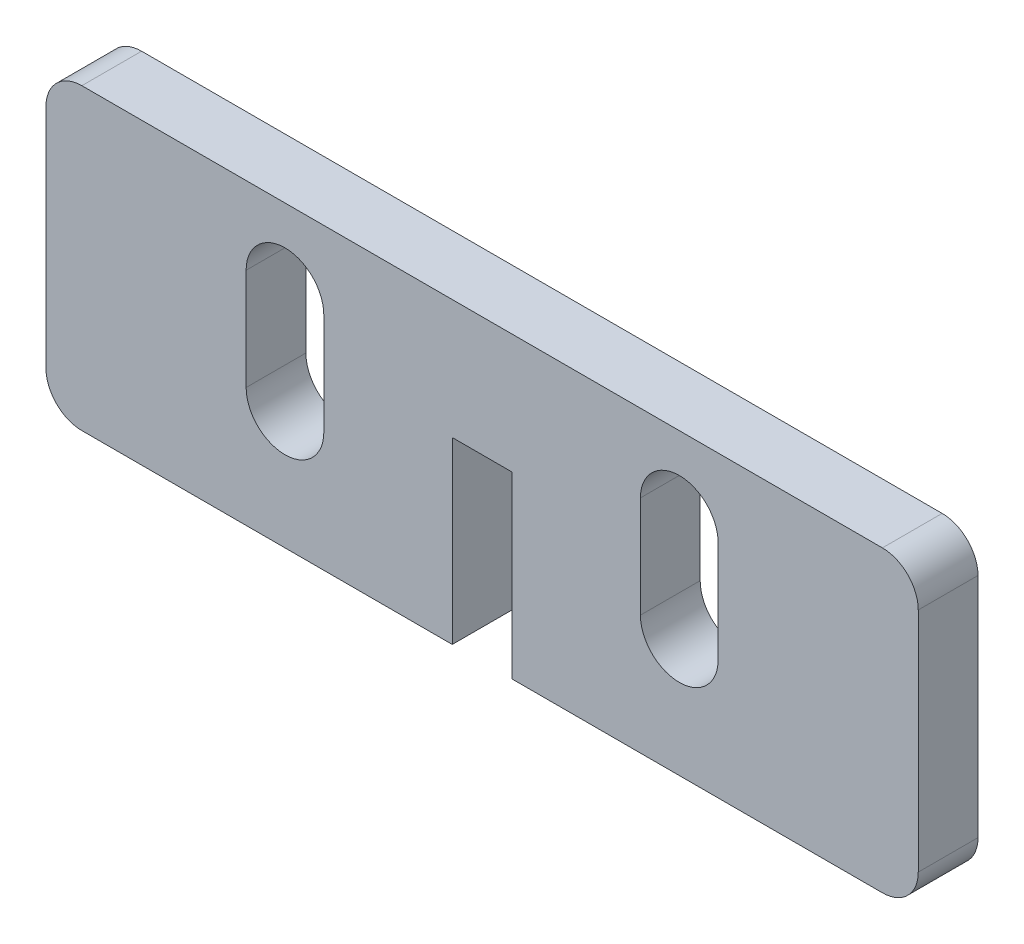
SolidWorks part; units mm, degrees
ref_plane "前视基准面" through (0, 0, 0) normal (0, 0, 1) x (1, 0, 0)
ref_plane "上视基准面" through (0, 0, 0) normal (0, 1, 0) x (1, 0, 0)
ref_plane "右视基准面" through (0, 0, 0) normal (1, 0, 0) x (0, 0, -1)
sketch "草图1" plane through (0, 0, 0) normal (0, 0, 1) x (1, 0, 0)
  line L0 (-16.5, -2.5) -> (-16.5, 6) construction
  line L1 (33.5, -12.5) -> (-33.5, -12.5) construction
  line L2 (36.5, -9.5) -> (36.5, 9.5)
  line L3 (33.5, 12.5) -> (-33.5, 12.5)
  line L4 (-36.5, -9.5) -> (-36.5, 9.5)
  line L5 (0, 12.5) -> (0, -12.5) construction
  line L6 (36.5, 0) -> (-36.5, 0) construction
  line L7 (2.5, 2.5) -> (-2.5, 2.5)
  line L8 (2.5, 2.5) -> (2.5, -12.5)
  line L9 (2.5, -12.5) -> (-2.5, -12.5) construction
  line L10 (-2.5, 2.5) -> (-2.5, -12.5)
  line L11 (0, -12.5) -> (0, 2.5) construction
  line L12 (2.5, -5) -> (-2.5, -5) construction
  line L13 (-19.75, -2.5) -> (-19.75, 6)
  line L14 (-13.25, -2.5) -> (-13.25, 6)
  line L15 (16.5, -2.5) -> (16.5, 6) construction
  line L16 (19.75, -2.5) -> (19.75, 6)
  line L17 (13.25, -2.5) -> (13.25, 6)
  line L18 (-33.5, -12.5) -> (-2.5, -12.5)
  line L19 (2.5, -12.5) -> (33.5, -12.5)
  arc A0 (-19.75, -2.5) -> (-13.25, -2.5) centre (-16.5, -2.5) ccw
  arc A1 (-13.25, 6) -> (-19.75, 6) centre (-16.5, 6) ccw
  arc A2 (19.75, -2.5) -> (13.25, -2.5) centre (16.5, -2.5) cw
  arc A3 (13.25, 6) -> (19.75, 6) centre (16.5, 6) cw
  arc A4 (33.5, -12.5) -> (36.5, -9.5) centre (33.5, -9.5) ccw
  arc A5 (-33.5, -12.5) -> (-36.5, -9.5) centre (-33.5, -9.5) cw
  arc A6 (36.5, 9.5) -> (33.5, 12.5) centre (33.5, 9.5) ccw
  arc A7 (-33.5, 12.5) -> (-36.5, 9.5) centre (-33.5, 9.5) ccw
  point P0 (0, 0)
  point P4 (0, -5)
  point P13 (-16.5, 1.75)
  point P21 (-16.5, 9.25)
  point P22 (-16.5, -5.75)
  point P25 (16.5, 1.75)
  point P32 (36.5, -12.5)
  point P37 (36.5, 12.5)
  point P40 (-36.5, 12.5)
  dimension "D9" = 3
  dimension "D1" = 73
  dimension "D2" = 25
  dimension "D3" = 5
  dimension "D4" = 15
  dimension "D5" = 3.25
  dimension "D6" = 10.75
  dimension "D7" = 6.5
  dimension "D8" = 15
extrude "凸台-拉伸1" add sketch "草图1" along normal blind 5
